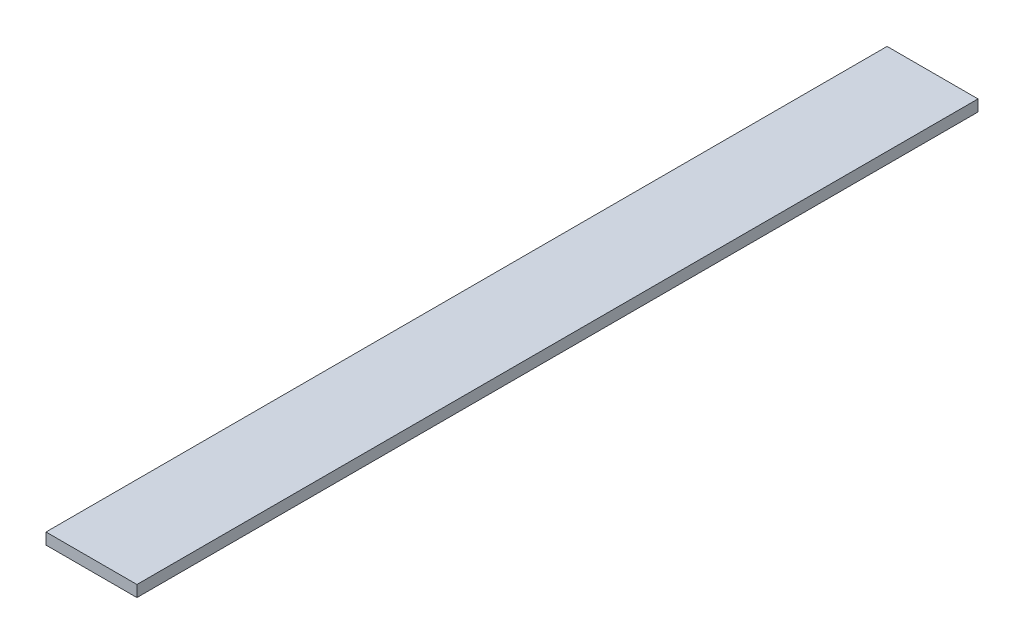
SolidWorks part; units mm, degrees
material "Glass"
ref_plane "Front Plane" through (0, 0, 0) normal (0, 0, 1) x (1, 0, 0)
ref_plane "Top Plane" through (0, 0, 0) normal (0, 1, 0) x (1, 0, 0)
ref_plane "Right Plane" through (0, 0, 0) normal (1, 0, 0) x (0, 0, -1)
sketch "Sketch1" plane through (0, 0, 0) normal (0, 1, 0) x (1, 0, 0)
  line L0 (-12.7, 117.475) -> (12.7, -117.475) construction
  line L1 (-12.7, 117.475) -> (12.7, 117.475)
  line L2 (-12.7, 117.475) -> (-12.7, -117.475)
  line L3 (-12.7, -117.475) -> (12.7, -117.475)
  line L4 (12.7, 117.475) -> (12.7, -117.475)
  dimension "D1" = 234.95
  dimension "D2" = 25.4
extrude "Boss-Extrude1" add sketch "Sketch1" along normal blind 3.175
